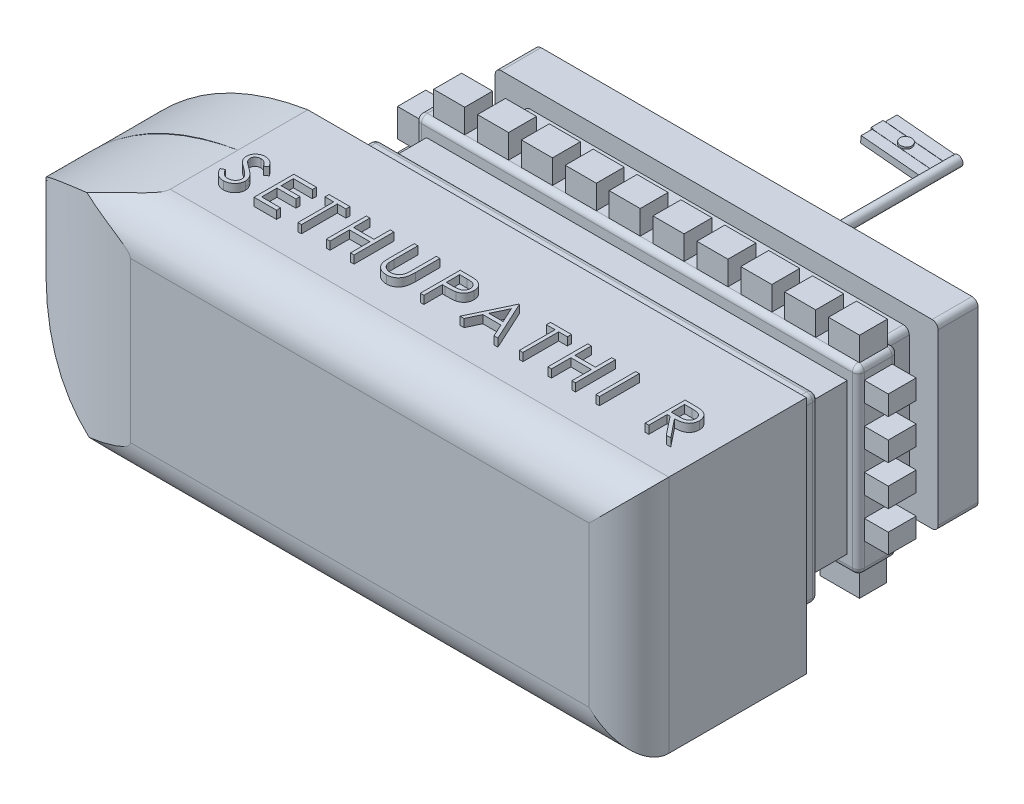
SolidWorks part; units mm, degrees
ref_plane "Front Plane" through (0, 0, 0) normal (0, 0, 1) x (1, 0, 0)
ref_plane "Top Plane" through (0, 0, 0) normal (0, 1, 0) x (1, 0, 0)
ref_plane "Right Plane" through (0, 0, 0) normal (1, 0, 0) x (0, 0, -1)
sketch "Sketch1" plane through (0, 0, 0) normal (0, 0, 1) x (1, 0, 0)
  line L0 (0, 0) -> (-216.8893, 0) construction
  line L1 (-125, -60) -> (125, -60)
  line L2 (-125, -60) -> (-125, 60)
  line L3 (-125, 60) -> (125, 60)
  line L4 (125, -60) -> (125, 60)
  line L5 (-125, -60) -> (125, 60) construction
  line L6 (-125, 60) -> (125, -60) construction
  spline S0 degree 2 poles (-216.8893, 0) (-184.9167, 49.4095) (-125, 60) knots 0 0 0 1 1 1
  spline S1 degree 2 poles (-216.8893, 0) (-185.8035, -45.859) (-125, -60) knots 0 0 0 1 1 1
  point P0 (0, 0)
  dimension "D1" = 250
  dimension "D2" = 120
extrude "Boss-Extrude1" add sketch "Sketch1" along normal blind 54 contours S0 S1 L2 | L1 L4 L3 L2
sketch "Sketch3" plane through (0, -60, 0) normal (0, -1, 0) x (1, 0, 0)
  line L0 (-216.8893, 0) -> (-216.8893, 54)
  line L1 (-216.8893, 54) -> (-125, 54)
  spline S0 degree 2 poles (-216.8893, 0) (-186.2243, 48.7177) (-125, 54) knots 0 0 0 1 1 1
extrude "Cut-Extrude1" cut sketch "Sketch3" against normal blind 156
sketch "Sketch4" plane through (0, 0, 0) normal (0, 0, -1) x (-1, 0, 0)
  line L1 (-117.1629, 53.7991) -> (117.1629, 53.7991)
  line L2 (-117.1629, 53.7991) -> (-117.1629, -53.7991)
  line L3 (-117.1629, -53.7991) -> (117.1629, -53.7991)
  line L5 (-117.1629, 53.7991) -> (117.1629, -53.7991) construction
  line L6 (-117.1629, -53.7991) -> (117.1629, 53.7991) construction
  line L7 (-125, 60) -> (125, 60)
  line L8 (-125, 60) -> (-125, -60)
  line L9 (-125, -60) -> (125, -60)
  line L11 (-125, 60) -> (125, -60) construction
  line L12 (-125, -60) -> (125, 60) construction
  spline S0 degree 2 poles (117.1629, 53.7991) (176.8406, 38.4593) (203.9603, 0) knots 0 0 0 1 1 1
  spline S1 degree 2 poles (117.1629, -53.7991) (166.588, -40.9852) (203.9603, 0) knots 0 0 0 1 1 1
  spline S2 degree 2 poles (125, 60) (183.3564, 50.5908) (216.8893, 0) knots 0 0 0 1 1 1
  spline S3 degree 2 poles (125, -60) (178.4771, -48.4646) (216.8893, 0) knots 0 0 0 1 1 1
  point P0 (0, 0)
  point P6 (0, 0)
extrude "Boss-Extrude2" add sketch "Sketch4" along normal blind 35
sketch "Sketch5" plane through (0, 0, 0) normal (0, 0, -1) x (-1, 0, 0)
  line L1 (-111.0426, 45.4532) -> (111.0426, 45.4532)
  line L2 (-111.0426, 45.4532) -> (-111.0426, -45.4532)
  line L3 (-111.0426, -45.4532) -> (111.0426, -45.4532)
  line L4 (111.0426, 45.4532) -> (111.0426, -45.4532)
  line L5 (-111.0426, 45.4532) -> (111.0426, -45.4532) construction
  line L6 (-111.0426, -45.4532) -> (111.0426, 45.4532) construction
  point P0 (0, 0)
extrude "Boss-Extrude3" add sketch "Sketch5" along normal blind 55
sketch "Sketch6" plane through (0, 0, -55) normal (0, 0, -1) x (-1, 0, 0)
  line L1 (-105.4787, 37.6637) -> (105.4787, 37.6637)
  line L2 (-105.4787, 37.6637) -> (-105.4787, -37.6637)
  line L3 (-105.4787, -37.6637) -> (105.4787, -37.6637)
  line L4 (105.4787, 37.6637) -> (105.4787, -37.6637)
  line L5 (-105.4787, 37.6637) -> (105.4787, -37.6637) construction
  line L6 (-105.4787, -37.6637) -> (105.4787, 37.6637) construction
  point P0 (0, 0)
extrude "Boss-Extrude4" add sketch "Sketch6" along normal blind 20
sketch "Sketch7" plane through (0, 0, -75) normal (0, 0, -1) x (-1, 0, 0)
  line L0 (111.0426, -45.4532) -> (111.0426, 45.4532) construction
  line L1 (-111.0426, 45.4532) -> (111.0426, 45.4532)
  line L2 (-111.0426, 45.4532) -> (-111.0426, -45.4532)
  line L3 (-111.0426, -45.4532) -> (111.0426, -45.4532)
  line L4 (111.0426, 45.4532) -> (111.0426, -45.4532)
  line L5 (-111.0426, 45.4532) -> (111.0426, -45.4532) construction
  line L6 (-111.0426, -45.4532) -> (111.0426, 45.4532) construction
  line L7 (111.0426, -45.4532) -> (111.0426, 45.4532) construction
  point P0 (0, 0)
extrude "Boss-Extrude5" add sketch "Sketch7" along normal blind 20
sketch "Sketch8" plane through (0, 0, -95) normal (0, 0, -1) x (-1, 0, 0)
  line L1 (-96.5764, 35.9946) -> (96.5764, 35.9946)
  line L2 (-96.5764, 35.9946) -> (-96.5764, -35.9946)
  line L3 (-96.5764, -35.9946) -> (96.5764, -35.9946)
  line L4 (96.5764, 35.9946) -> (96.5764, -35.9946)
  line L5 (-96.5764, 35.9946) -> (96.5764, -35.9946) construction
  line L6 (-96.5764, -35.9946) -> (96.5764, 35.9946) construction
  point P0 (0, 0)
extrude "Boss-Extrude6" add sketch "Sketch8" along normal blind 20
sketch "Sketch9" plane through (0, 0, -115) normal (0, 0, -1) x (-1, 0, 0)
  line L0 (-111.0426, -45.4532) -> (111.0426, -45.4532) construction
  line L1 (-111.0426, 45.4532) -> (111.0426, 45.4532)
  line L2 (-111.0426, 45.4532) -> (-111.0426, -45.4532)
  line L3 (-111.0426, -45.4532) -> (111.0426, -45.4532)
  line L4 (111.0426, 45.4532) -> (111.0426, -45.4532)
  line L5 (-111.0426, 45.4532) -> (111.0426, -45.4532) construction
  line L6 (-111.0426, -45.4532) -> (111.0426, 45.4532) construction
  point P0 (0, 0)
extrude "Boss-Extrude7" add sketch "Sketch9" along normal blind 20
fillet "Fillet1" radius 3 24 edges at (-111.0426, 0, -95) (-111.0426, 0, -75) (-111.0426, 45.4532, -85) (0, 45.4532, -95) (0, 45.4532, -75) (111.0426, 45.4532, -85) (111.0426, 0, -95) (111.0426, 0, -75) (111.0426, -45.4532, -85) (0, -45.4532, -95) (-111.0426, -45.4532, -85) (0, -45.4532, -75) (111.0426, -45.4532, -27.5) (111.0426, 45.4532, -27.5) (111.0426, 0, -55) (0, 45.4532, -55) (-111.0426, 45.4532, -27.5) (-111.0426, -45.4532, -27.5) (-111.0426, 0, -55) (0, -45.4532, -55) (-96.5764, 35.9946, -105) (96.5764, 35.9946, -105) (96.5764, -35.9946, -105) (-96.5764, -35.9946, -105)
fillet "Fillet2" radius 20 3 edges at (0, -60, 54) (125, 0, 54) (0, 60, 54)
fillet "Fillet4" radius 3 4 edges at (111.0426, -45.4532, -125) (111.0426, 45.4532, -125) (-111.0426, -45.4532, -125) (-111.0426, 45.4532, -125)
sketch "Sketch10" plane through (0, 45.4532, 0) normal (0, 1, 0) x (1, 0, 0)
  line L0 (-108.0426, 85) -> (108.0426, 85) construction
  line L1 (-108.0426, 92) -> (-108.0426, 78) construction
  line L2 (108.0426, 78) -> (108.0426, 92) construction
  line L3 (-111.0426, 125) -> (111.0426, 125) construction
  line L4 (-111.0426, 115) -> (-111.0426, 135) construction
  line L5 (111.0426, 135) -> (111.0426, 115) construction
  line L6 (-108.0426, 78) -> (108.0426, 78) construction
  line L7 (-104.9223, 92) -> (-89.3433, 92)
  line L8 (-104.9223, 92) -> (-104.9223, 78)
  line L9 (-104.9223, 78) -> (-89.3433, 78)
  line L10 (-89.3433, 92) -> (-89.3433, 78)
  line L11 (-104.9223, 92) -> (-89.3433, 78) construction
  line L12 (-104.9223, 78) -> (-89.3433, 92) construction
  line L13 (-82.9223, 92) -> (-82.9223, 78)
  line L14 (-82.9223, 92) -> (-67.3433, 92)
  line L15 (-67.3433, 92) -> (-67.3433, 78)
  line L16 (-82.9223, 78) -> (-67.3433, 78)
  line L17 (-60.9223, 92) -> (-60.9223, 78)
  line L18 (-60.9223, 92) -> (-45.3433, 92)
  line L19 (-45.3433, 92) -> (-45.3433, 78)
  line L20 (-60.9223, 78) -> (-45.3433, 78)
  line L21 (-38.9223, 92) -> (-38.9223, 78)
  line L22 (-38.9223, 92) -> (-23.3433, 92)
  line L23 (-23.3433, 92) -> (-23.3433, 78)
  line L24 (-38.9223, 78) -> (-23.3433, 78)
  line L25 (-16.9223, 92) -> (-16.9223, 78)
  line L26 (-16.9223, 92) -> (-1.3433, 92)
  line L27 (-1.3433, 92) -> (-1.3433, 78)
  line L28 (-16.9223, 78) -> (-1.3433, 78)
  line L29 (5.0777, 92) -> (5.0777, 78)
  line L30 (5.0777, 92) -> (20.6567, 92)
  line L31 (20.6567, 92) -> (20.6567, 78)
  line L32 (5.0777, 78) -> (20.6567, 78)
  line L33 (27.0777, 92) -> (27.0777, 78)
  line L34 (27.0777, 92) -> (42.6567, 92)
  line L35 (42.6567, 92) -> (42.6567, 78)
  line L36 (27.0777, 78) -> (42.6567, 78)
  line L37 (49.0777, 92) -> (49.0777, 78)
  line L38 (49.0777, 92) -> (64.6567, 92)
  line L39 (64.6567, 92) -> (64.6567, 78)
  line L40 (49.0777, 78) -> (64.6567, 78)
  line L41 (71.0777, 92) -> (71.0777, 78)
  line L42 (71.0777, 92) -> (86.6567, 92)
  line L43 (86.6567, 92) -> (86.6567, 78)
  line L44 (71.0777, 78) -> (86.6567, 78)
  line L45 (93.0777, 92) -> (93.0777, 78)
  line L46 (93.0777, 92) -> (108.6567, 92)
  line L47 (108.6567, 92) -> (108.6567, 78)
  line L48 (93.0777, 78) -> (108.6567, 78)
  point P12 (-97.1328, 85)
  dimension "D1" = 10
extrude "Boss-Extrude8" add sketch "Sketch10" along normal blind 12
sketch "Sketch11" plane through (111.0426, 0, 0) normal (1, 0, 0) x (0, 0, -1)
  line L0 (92, 19.0923) -> (92, 9.2497)
  line L1 (78, 39.0923) -> (92, 39.0923)
  line L2 (78, 39.0923) -> (78, 29.2497)
  line L3 (78, 29.2497) -> (92, 29.2497)
  line L4 (92, 39.0923) -> (92, 29.2497)
  line L5 (78, 39.0923) -> (92, 29.2497) construction
  line L6 (78, 29.2497) -> (92, 39.0923) construction
  line L7 (78, 19.0923) -> (92, 19.0923)
  line L8 (78, 19.0923) -> (78, 9.2497)
  line L9 (78, 9.2497) -> (92, 9.2497)
  line L10 (92, -0.9077) -> (92, -10.7503)
  line L11 (78, -0.9077) -> (92, -0.9077)
  line L12 (78, -0.9077) -> (78, -10.7503)
  line L13 (78, -10.7503) -> (92, -10.7503)
  line L14 (92, -20.9077) -> (92, -30.7503)
  line L15 (78, -20.9077) -> (92, -20.9077)
  line L16 (78, -20.9077) -> (78, -30.7503)
  line L17 (78, -30.7503) -> (92, -30.7503)
  point P0 (85, 34.171)
  dimension "D1" = 4
extrude "Boss-Extrude10" add sketch "Sketch11" along normal blind 12
sketch "Sketch12" plane through (0, -45.4532, 0) normal (0, -1, 0) x (1, 0, 0)
  line L0 (53.2797, -78.5793) -> (53.2797, -92)
  line L1 (88.2797, -78.5793) -> (108.0426, -78.5793)
  line L2 (88.2797, -78.5793) -> (88.2797, -92)
  line L3 (88.2797, -92) -> (108.0426, -92)
  line L4 (108.0426, -78.5793) -> (108.0426, -92)
  line L5 (88.2797, -78.5793) -> (108.0426, -92) construction
  line L6 (88.2797, -92) -> (108.0426, -78.5793) construction
  line L7 (53.2797, -78.5793) -> (73.0426, -78.5793)
  line L8 (73.0426, -78.5793) -> (73.0426, -92)
  line L9 (53.2797, -92) -> (73.0426, -92)
  line L10 (18.2797, -78.5793) -> (18.2797, -92)
  line L11 (18.2797, -78.5793) -> (38.0426, -78.5793)
  line L12 (38.0426, -78.5793) -> (38.0426, -92)
  line L13 (18.2797, -92) -> (38.0426, -92)
  line L14 (-16.7203, -78.5793) -> (-16.7203, -92)
  line L15 (-16.7203, -78.5793) -> (3.0426, -78.5793)
  line L16 (3.0426, -78.5793) -> (3.0426, -92)
  line L17 (-16.7203, -92) -> (3.0426, -92)
  line L18 (-51.7203, -78.5793) -> (-51.7203, -92)
  line L19 (-51.7203, -78.5793) -> (-31.9574, -78.5793)
  line L20 (-31.9574, -78.5793) -> (-31.9574, -92)
  line L21 (-51.7203, -92) -> (-31.9574, -92)
  line L22 (-86.7203, -78.5793) -> (-86.7203, -92)
  line L23 (-86.7203, -78.5793) -> (-66.9574, -78.5793)
  line L24 (-66.9574, -78.5793) -> (-66.9574, -92)
  line L25 (-86.7203, -92) -> (-66.9574, -92)
  point P0 (98.1611, -85.2896)
  dimension "D1" = 6
extrude "Boss-Extrude11" add sketch "Sketch12" along normal blind 12
sketch "Sketch13" plane through (-111.0426, 0, 0) normal (-1, 0, 0) x (0, 0, 1)
  line L0 (-78, -42.4532) -> (-78, 42.4532) construction
  line L1 (-92.1982, 40.9378) -> (-78, 40.9378)
  line L2 (-92.1982, 40.9378) -> (-92.1982, 26.7891)
  line L3 (-92.1982, 26.7891) -> (-78, 26.7891)
  line L4 (-78, 40.9378) -> (-78, 26.7891)
  line L5 (-92.1982, 40.9378) -> (-78, 26.7891) construction
  line L6 (-92.1982, 26.7891) -> (-78, 40.9378) construction
  line L7 (-92.1982, 20.9378) -> (-78, 20.9378)
  line L8 (-92.1982, 20.9378) -> (-92.1982, 6.7891)
  line L9 (-92.1982, 6.7891) -> (-78, 6.7891)
  line L10 (-78, 20.9378) -> (-78, 6.7891)
  line L11 (-92.1982, 0.9378) -> (-78, 0.9378)
  line L12 (-92.1982, 0.9378) -> (-92.1982, -13.2109)
  line L13 (-92.1982, -13.2109) -> (-78, -13.2109)
  line L14 (-78, 0.9378) -> (-78, -13.2109)
  line L15 (-92.1982, -19.0622) -> (-78, -19.0622)
  line L16 (-92.1982, -19.0622) -> (-92.1982, -33.2109)
  line L17 (-92.1982, -33.2109) -> (-78, -33.2109)
  line L18 (-78, -19.0622) -> (-78, -33.2109)
  point P0 (-85.0991, 33.8634)
  dimension "D1" = 4
extrude "Boss-Extrude12" add sketch "Sketch13" along normal blind 12
sketch "Sketch16" plane through (0, 0, -135) normal (0, 0, -1) x (-1, 0, 0)
  circle A0 centre (0, 0) radius 28.0707
extrude "Boss-Extrude13" add sketch "Sketch16" along normal blind 5
sketch "Sketch17" plane through (0, 0, -140) normal (0, 0, -1) x (-1, 0, 0)
  line L0 (1.9719, -1.5368) -> (1.658, 1.8711)
  arc A0 (1.658, 1.8711) -> (1.9719, -1.5368) centre (0, 0) ccw
  dimension "D1" = 5
extrude "Boss-Extrude15" add sketch "Sketch17" along normal blind 96
sketch "Sketch18" plane through (-1.8149, 0.1672, 0) normal (-0.9958, 0.0917, 0) x (0, 0, 1)
  line L0 (-236, -1.7112) -> (-140, -1.7112) construction
  line L1 (-236, 1.7112) -> (-230, 1.7112)
  line L2 (-236, 1.7112) -> (-236, -1.7112)
  line L3 (-236, -1.7112) -> (-230, -1.7112)
  line L4 (-230, 1.7112) -> (-230, -1.7112)
  line L5 (-230, 1.7112) -> (-236, -1.7112) construction
  line L6 (-236, 1.7112) -> (-230, -1.7112) construction
  point P6 (-233, 0)
  dimension "D1" = 6
extrude "Boss-Extrude16" add sketch "Sketch18" along normal blind 29
sketch "Sketch20" plane through (-1.8149, 0.1672, 0) normal (-0.9958, 0.0917, 0) x (0, 0, 1)
  line L0 (-230, -1.7112) -> (-140, -1.7112) construction
  line L1 (-230, 1.7112) -> (-224, 1.7112)
  line L2 (-230, 1.7112) -> (-230, -1.7112)
  line L3 (-230, -1.7112) -> (-224, -1.7112)
  line L4 (-224, 1.7112) -> (-224, -1.7112)
  dimension "D1" = 6
extrude "Boss-Extrude18" add sketch "Sketch20" along normal blind 30
sketch "Sketch21" plane through (-1.8149, 0.1672, 0) normal (-0.9958, 0.0917, 0) x (0, 0, 1)
  line L0 (-224, -1.7112) -> (-140, -1.7112) construction
  line L1 (-224, 1.7112) -> (-218, 1.7112)
  line L2 (-224, 1.7112) -> (-224, -1.7112)
  line L3 (-224, -1.7112) -> (-218, -1.7112)
  line L4 (-218, 1.7112) -> (-218, -1.7112)
  dimension "D1" = 6
extrude "Boss-Extrude19" add sketch "Sketch21" along normal blind 29
sketch "Sketch22" plane through (-0.157, -1.704, 0) normal (-0.0917, -0.9958, 0) x (0.9958, -0.0917, 0)
  line L0 (-30.8226, -224) -> (-30.8226, -218) construction
  line L1 (-30.8226, -223.5226) -> (-1.8226, -223.5226)
  line L2 (-30.8226, -223.5226) -> (-30.8226, -223.6193)
  line L3 (-30.8226, -223.6193) -> (-1.8226, -223.6193)
  line L4 (-1.8226, -223.5226) -> (-1.8226, -223.6193)
  line L5 (-1.8226, -236) -> (-1.8226, -218) construction
  line L7 (-30.8226, -230) -> (-1.8226, -230)
  line L8 (-30.8226, -230) -> (-30.8226, -230.1177)
  line L9 (-30.8226, -230.1177) -> (-1.8226, -230.1177)
  line L10 (-1.8226, -230) -> (-1.8226, -230.1177)
extrude "Cut-Extrude2" cut sketch "Sketch22" against normal blind 29
sketch "Sketch23" plane through (0.157, 1.704, 0) normal (0.0917, 0.9958, 0) x (0.9958, -0.0917, 0)
  circle A0 centre (-17.1924, 226.8263) radius 2.9742
extrude "Boss-Extrude21" add sketch "Sketch23" along normal blind 1 and the other way blind 5
sketch "Sketch24" plane through (0, 60, 0) normal (0, 1, 0) x (1, 0, 0)
  line L0 (-118.0139, -20.463) -> (117.1273, -20.463) construction
  text T0 "SETHUPATHI R" font "Century Gothic" height 20
extrude "Boss-Extrude22" add sketch "Sketch24" along normal blind 4
